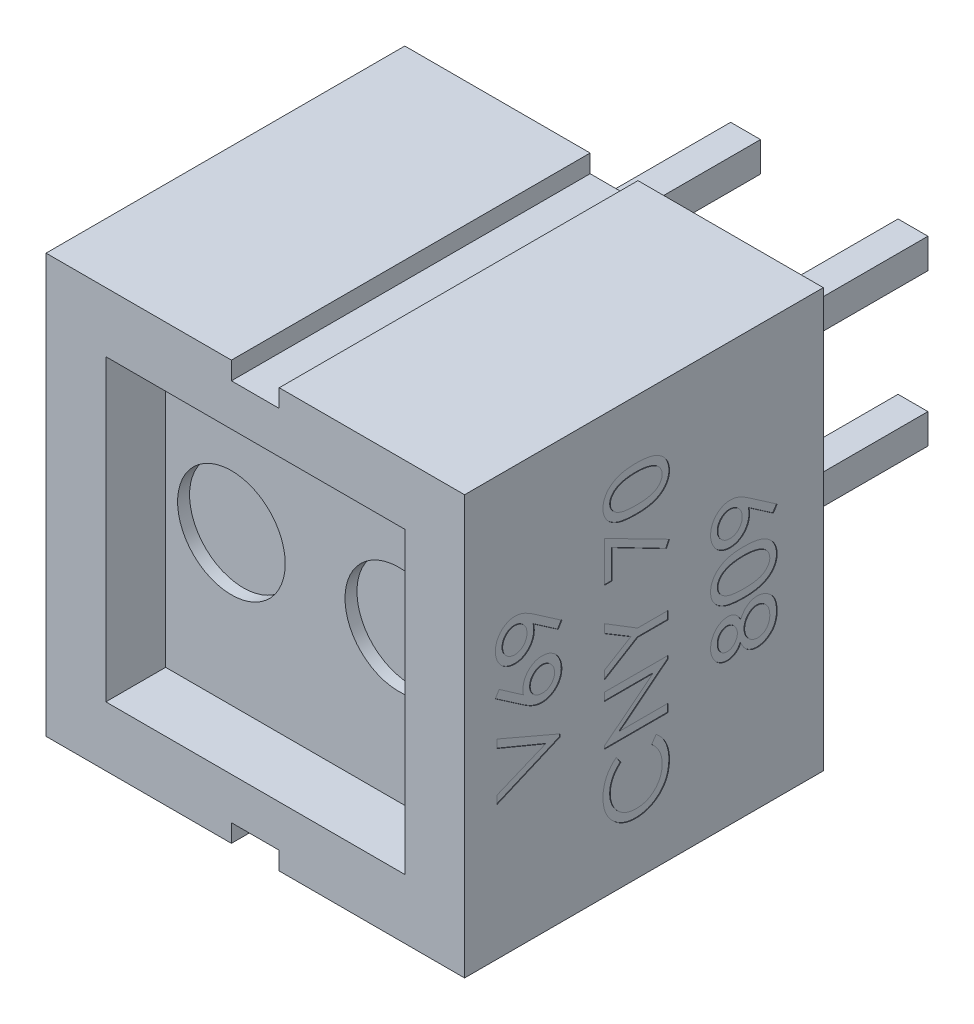
SolidWorks part; units mm, degrees
ref_plane "Plan de face" through (0, 0, 0) normal (0, 0, 1) x (1, 0, 0)
ref_plane "Plan de dessus" through (0, 0, 0) normal (0, 1, 0) x (1, 0, 0)
ref_plane "Plan de droite" through (0, 0, 0) normal (1, 0, 0) x (0, 0, -1)
sketch "Esquisse1" plane through (0, 0, 0) normal (0, 0, 1) x (1, 0, 0)
  line L0 (0, 0) -> (0, 3.2)
  line L1 (0, 3.2) -> (0.4, 3.2)
  line L2 (0.4, 3.2) -> (0.4, 3.5)
  line L3 (0.4, 3.5) -> (3.5, 3.5)
  line L4 (3.5, 3.5) -> (3.5, 0)
  line L5 (3.5, 0) -> (0, 0)
  dimension "D1" = 3.5
  dimension "D2" = 3.5
  dimension "D3" = 0.4
  dimension "D4" = 0.3
extrude "Boss.-Extru.1" add sketch "Esquisse1" along normal blind 6
sketch "Esquisse2" plane through (0, 0, 6) normal (0, 0, 1) x (1, 0, 0)
  line L0 (3.5, 0) -> (3.5, 3.5) construction
  line L1 (0, 0) -> (2.5, 0)
  line L2 (0, 0) -> (0, 2.5)
  line L3 (0, 2.5) -> (2.5, 2.5)
  line L4 (2.5, 0) -> (2.5, 2.5)
  line L5 (3.5, 3.5) -> (0.4, 3.5) construction
  dimension "D1" = 1
  dimension "D2" = 1
extrude "Enlèv. mat.-Extru.1" cut sketch "Esquisse2" against normal blind 1
sketch "Esquisse3" plane through (0, 0, 0) normal (0, 0, -1) x (-1, 0, 0)
  line L0 (-1.4, 1.52) -> (-1.4, 1.02) construction
  line L1 (-1.65, 1.02) -> (-1.15, 1.02)
  line L2 (-1.65, 1.02) -> (-1.65, 1.52)
  line L3 (-1.65, 1.52) -> (-1.15, 1.52)
  line L4 (-1.15, 1.02) -> (-1.15, 1.52)
  line L5 (-1.65, 1.27) -> (-1.15, 1.27) construction
  line L6 (0, 3.2) -> (0, 0) construction
  line L7 (0, 0) -> (-3.5, 0) construction
  point P8 (-1.4, 1.27)
  dimension "D1" = 0.5
  dimension "D2" = 0.5
  dimension "D3" = 1.4
  dimension "D4" = 1.27
extrude "Boss.-Extru.2" add sketch "Esquisse3" along normal blind 3.6
mirror "Symétrie1" of "Boss.-Extru.1", "Boss.-Extru.2", "Enlèv. mat.-Extru.1"
mirror "Symétrie3" of "Boss.-Extru.2", "Symétrie1", "Enlèv. mat.-Extru.1", "Boss.-Extru.1"
sketch "Esquisse4" plane through (0, 0, 5) normal (0, 0, 1) x (1, 0, 0)
  line L0 (-2.5, 0) -> (2.5, 0) construction
  line L1 (-2.5, -2.5) -> (-2.5, 2.5) construction
  line L2 (2.5, -2.5) -> (2.5, 2.5) construction
  circle A0 centre (-1.4, 0) radius 0.9
  circle A1 centre (1.4, 0) radius 0.9
  dimension "D3" = 1.8
  dimension "D1" = 1.4
  dimension "D2" = 1.4
extrude "Enlèv. mat.-Extru.2" cut sketch "Esquisse4" against normal blind 0.2
sketch "Esquisse5" plane through (3.5, 0, 0) normal (1, 0, 0) x (0, 0, -1)
  line L0 (-2.6, -2.7) -> (-2.6, 3.5) construction
  line L2 (-6, 3.5) -> (0, 3.5) construction
  line L3 (-6, -3.5) -> (0, -3.5) construction
  line L4 (0, -3.5) -> (0, 3.5) construction
  line L5 (-4.4, -1.3) -> (-4.4, 3.5) construction
  line L6 (-0.8, -1.2) -> (-0.8, 3.5) construction
  text T0 "CNY 70" font "Century Gothic" height in points 4
  text T1 "V69" font "Century Gothic" height in points 4
  text T2 "809" font "Century Gothic" height in points 4
  dimension "D1" = 0.8
  dimension "D2" = 2.6
  dimension "D3" = 1.8
  dimension "D4" = 1.8
  dimension "D5" = 2.2
  dimension "D6" = 2.3
extrude "Enlèv. mat.-Extru.3" cut sketch "Esquisse5" against normal blind 0.01
